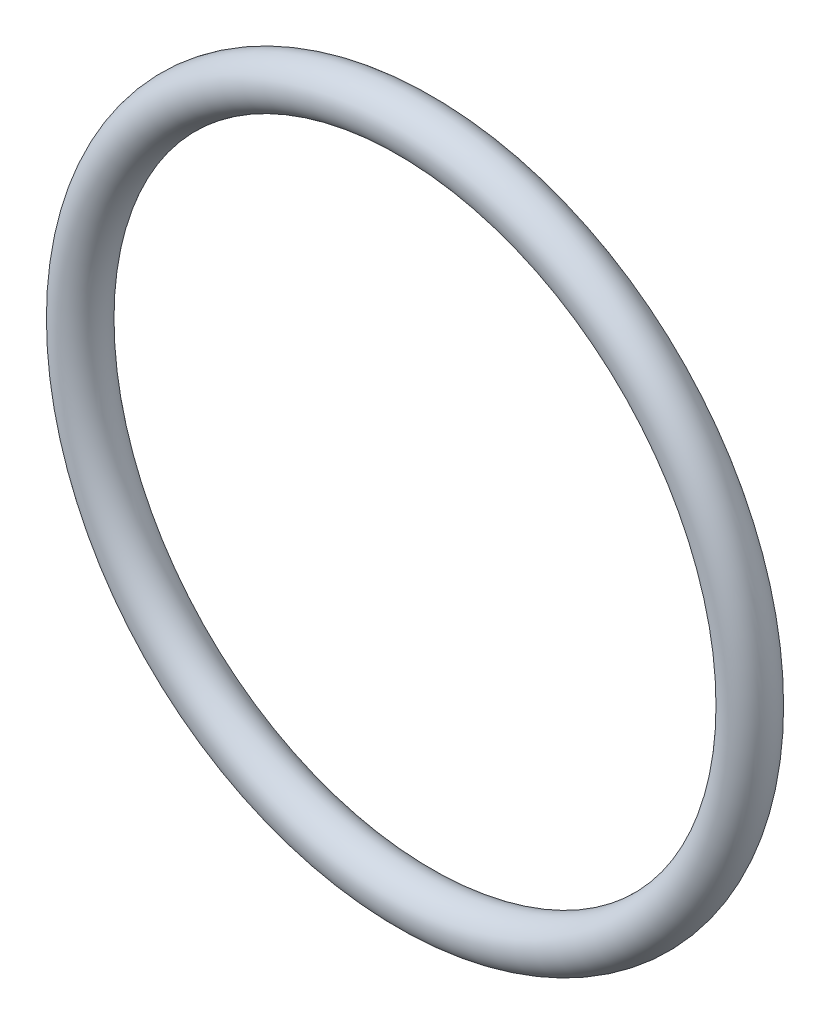
SolidWorks part; units mm, degrees
ref_plane "Front" through (0, 0, 0) normal (0, 0, 1) x (1, 0, 0)
ref_plane "Top" through (0, 0, 0) normal (0, 1, 0) x (1, 0, 0)
ref_plane "Right" through (0, 0, 0) normal (1, 0, 0) x (0, 0, -1)
sketch "Sketch1" plane through (0, 0, 0) normal (0, 0, 1) x (1, 0, 0)
  circle A0 centre (0, 0) radius 6.5 construction
  circle A1 centre (0, 0) radius 7.5 construction
  point P4 (6.5, 0)
  point P5 (7.5, 0)
  dimension "ID" = 13
  dimension "OD" = 15
sketch "Sketch2" plane through (0, 0, 0) normal (1, 0, 0) x (0, 0, -1)
  line L0 (-0.5, 0) -> (0.5, 0) construction
  dimension "Width" = 1
sketch "Sketch3" plane through (0, 0, 0) normal (0, 1, 0) x (1, 0, 0)
  line L2 (0, -0.5) -> (0, 0.5) construction
  line L7 (7, -0.5) -> (7, 0.5) construction
  circle A0 centre (7, 0) radius 0.5
revolve "Revolve1" add sketch "Sketch3" angle 360 about L0
sketch "Sketch5" plane through (0, 0, 0) normal (0, 0, 1) x (1, 0, 0)
  circle A0 centre (0, 0) radius 3.9524
